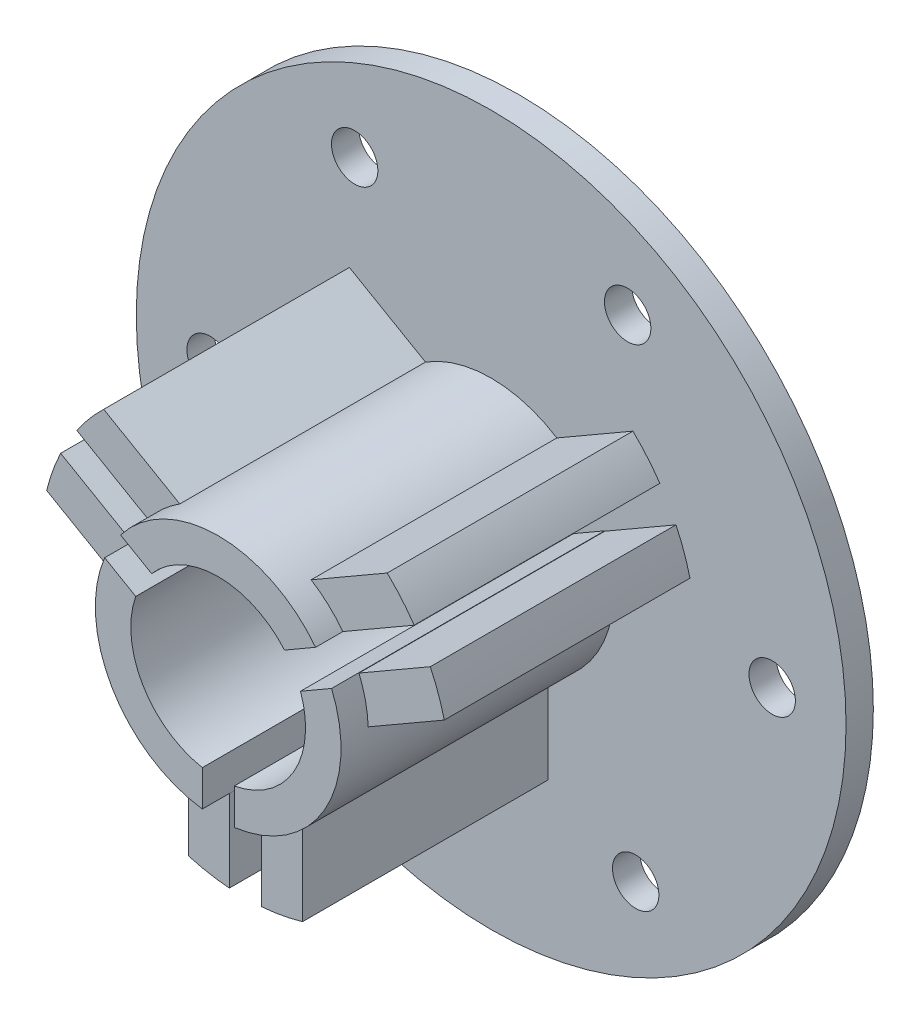
SolidWorks part; units mm, degrees
material "PF"
ref_plane "Front Plane" through (0, 0, 0) normal (0, 0, 1) x (1, 0, 0)
ref_plane "Top Plane" through (0, 0, 0) normal (0, 1, 0) x (1, 0, 0)
ref_plane "Right Plane" through (0, 0, 0) normal (1, 0, 0) x (0, 0, -1)
ref_plane "Plane1" through (0, 0, 5) normal (0, 0, 1) x (1, 0, 0)
sketch "Sketch1" plane through (0, 0, 5) normal (0, 0, 1) x (1, 0, 0)
  circle A0 centre (0, 0) radius 65
  dimension "D1" = 130
extrude "Boss-Extrude1" add sketch "Sketch1" against normal blind 5
sketch "Sketch2" plane through (0, 0, 5) normal (0, 0, 1) x (1, 0, 0)
  line L0 (-2.8966, -15.7407) -> (-2.8966, -22.3128)
  line L1 (-20.7924, 8.5981) -> (-15.0983, 5.3106)
  line L2 (17.8424, 13.7077) -> (12.1483, 10.4202)
  line L3 (-12.1836, 10.3789) -> (-17.8751, 13.6649)
  line L4 (2.95, -22.3058) -> (2.95, -15.7308)
  line L5 (15.0802, 5.3618) -> (20.7717, 8.6478)
  arc A0 (-2.8966, -22.3128) -> (-20.7924, 8.5981) centre (0, 0) cw
  arc A1 (-15.0983, 5.3106) -> (-2.8966, -15.7407) centre (0, 0) ccw
  arc A3 (-17.8751, 13.6649) -> (17.8424, 13.7077) centre (0, 0) cw
  arc A4 (12.1483, 10.4202) -> (-12.1836, 10.3789) centre (0, 0) ccw
  arc A5 (20.7717, 8.6478) -> (2.95, -22.3058) centre (0, 0) cw
  arc A6 (2.95, -15.7308) -> (15.0802, 5.3618) centre (0, 0) ccw
  point P17 (0, 0)
  dimension "D1" = 22.5
  dimension "D4" = 16.005
  dimension "D6" = 0
  dimension "D2" = 6.5749
  dimension "D3" = 6.572
  dimension "D5" = 15.0983
  dimension "D8" = 0
  dimension "D7" = 3
extrude "Boss-Extrude2" add sketch "Sketch2" along normal blind 50
sketch "Sketch3" plane through (0, 0, 5) normal (0, 0, 1) x (1, 0, 0)
  line L0 (-33.8503, 16.1371) -> (-20.7924, 8.5981)
  line L1 (-22.4815, 0.9131) -> (-36.4145, 8.9573)
  arc A0 (-20.7924, 8.5981) -> (-22.4815, 0.9131) centre (0, 0) ccw
  arc A1 (-36.4145, 8.9573) -> (-33.8503, 16.1371) centre (0, 0) cw
extrude "Boss-Extrude3" add sketch "Sketch3" along normal blind 45
sketch "Sketch4" plane through (0, 0, 5) normal (0, 0, 1) x (1, 0, 0)
  line L0 (-10.45, -36.0145) -> (-10.45, -19.9261)
  line L1 (-2.95, -22.3058) -> (-2.95, -37.3838)
  arc A0 (-10.45, -19.9261) -> (-2.95, -22.3058) centre (0, 0) ccw
  arc A1 (-2.95, -37.3838) -> (-10.45, -36.0145) centre (0, 0) cw
extrude "Boss-Extrude4" add sketch "Sketch4" along normal blind 45
sketch "Sketch5" plane through (0, 0, 5) normal (0, 0, 1) x (1, 0, 0)
  line L0 (-12.4081, 10.5702) -> (-17.8424, 13.7077)
  line L1 (17.8424, 13.7077) -> (12.4081, 10.5702)
  arc A0 (-17.8424, 13.7077) -> (17.8424, 13.7077) centre (0, 0) cw
  arc A1 (12.4081, 10.5702) -> (-12.4081, 10.5702) centre (0, 0) ccw
sketch "Sketch6" plane through (0, 0, 5) normal (0, 0, 1) x (1, 0, 0)
  line L0 (30.9003, 21.2467) -> (17.8424, 13.7077)
  line L1 (12.0315, 19.013) -> (25.9645, 27.0572)
  arc A0 (17.8424, 13.7077) -> (12.0315, 19.013) centre (0, 0) ccw
  arc A1 (25.9645, 27.0572) -> (30.9003, 21.2467) centre (0, 0) cw
extrude "Boss-Extrude6" add sketch "Sketch6" along normal blind 45
sketch "Sketch7" plane through (0, 0, 5) normal (0, 0, 1) x (1, 0, 0)
  line L0 (-25.9645, 27.0572) -> (-12.0315, 19.013)
  line L1 (-17.8424, 13.7077) -> (-30.9003, 21.2467)
  arc A0 (-30.9003, 21.2467) -> (-25.9645, 27.0572) centre (0, 0) cw
  arc A1 (-12.0315, 19.013) -> (-17.8424, 13.7077) centre (0, 0) ccw
extrude "Boss-Extrude7" add sketch "Sketch7" along normal blind 45
sketch "Sketch9" plane through (0, 0, 5) normal (0, 0, 1) x (1, 0, 0)
  line L0 (2.95, -37.3838) -> (2.95, -22.3058)
  line L1 (10.45, -19.9261) -> (10.45, -36.0145)
  arc A0 (2.95, -22.3058) -> (10.45, -19.9261) centre (0, 0) ccw
  arc A1 (10.45, -36.0145) -> (2.95, -37.3838) centre (0, 0) cw
extrude "Boss-Extrude9" add sketch "Sketch9" along normal blind 45
sketch "Sketch10" plane through (0, 0, 5) normal (0, 0, 1) x (1, 0, 0)
  line L0 (36.4145, 8.9573) -> (22.4815, 0.9131)
  line L1 (20.7924, 8.5981) -> (33.8503, 16.1371)
  arc A0 (22.4815, 0.9131) -> (20.7924, 8.5981) centre (0, 0) ccw
  arc A1 (33.8503, 16.1371) -> (36.4145, 8.9573) centre (0, 0) cw
extrude "Boss-Extrude10" add sketch "Sketch10" along normal blind 45
sketch "Sketch11" plane through (0, 0, 5) normal (0, 0, 1) x (1, 0, 0)
  line L0 (-51.4711, -0.8494) -> (-26.4711, -44.1506) construction
  line L1 (-38.9711, -22.5) -> (0, 0) construction
  circle A3 centre (-25, 45) radius 4.25
  circle A4 centre (25, 45) radius 4.25
  circle A5 centre (26.4711, -44.1506) radius 4.25
  circle A6 centre (51.4711, -0.8494) radius 4.25
  circle A7 centre (-51.4711, -0.8494) radius 4.25
  circle A8 centre (-26.4711, -44.1506) radius 4.25
  point P11 (-3.1475, 0)
  point P20 (0, 0)
  dimension "D1" = 8.5
  dimension "D2" = 8.5
  dimension "D3" = 45
  dimension "D4" = 25
  dimension "D5" = 25
  dimension "D6" = 45
  dimension "D8" = 45
  dimension "D7" = 3
extrude "Cut-Extrude1" cut sketch "Sketch11" against normal blind 10
